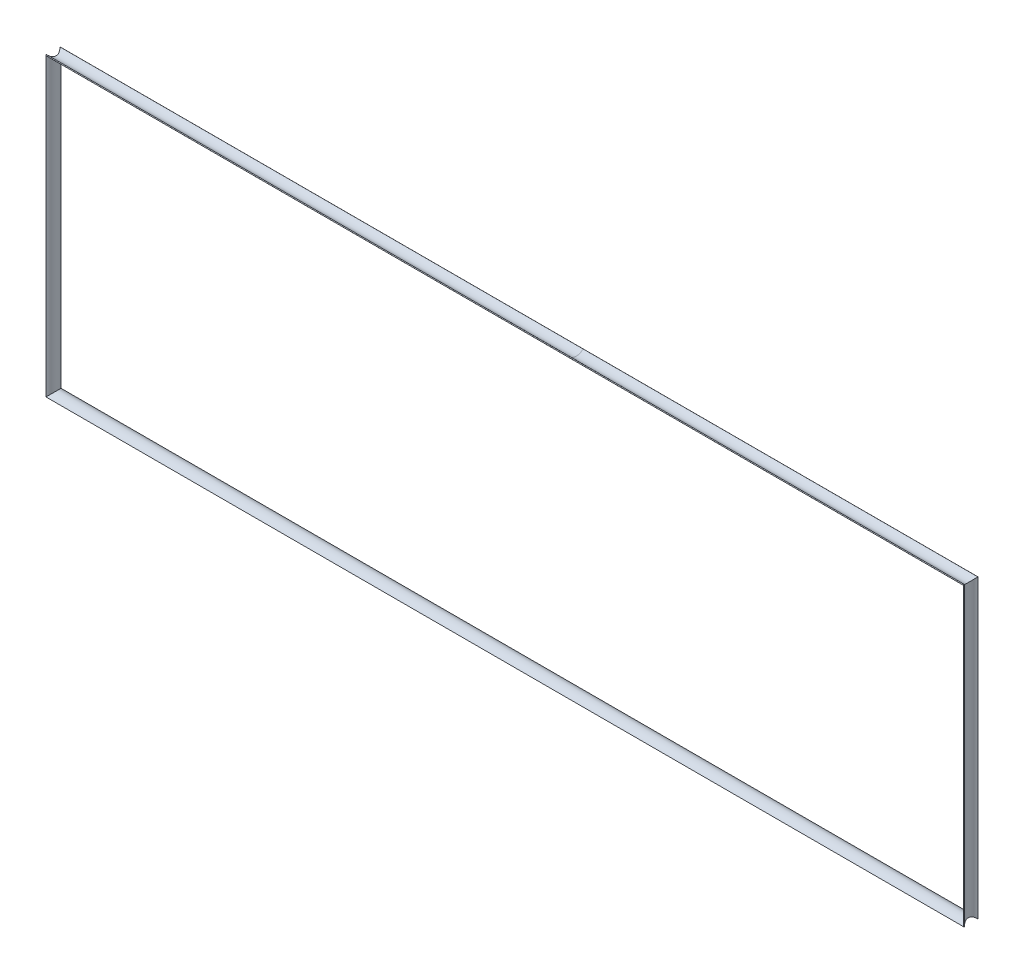
SolidWorks part; units mm, degrees
ref_plane "Front Plane" through (0, 0, 0) normal (0, 0, 1) x (1, 0, 0)
ref_plane "Top Plane" through (0, 0, 0) normal (0, 1, 0) x (1, 0, 0)
ref_plane "Right Plane" through (0, 0, 0) normal (1, 0, 0) x (0, 0, -1)
sketch "Sketch6" plane through (0, 0, 0) normal (0, 0, 1) x (1, 0, 0)
  line L0 (-194.9333, 26.8762) -> (-194.9333, -83.1238)
  line L1 (-194.9333, -83.1238) -> (147.0667, -83.1238)
  line L2 (147.0667, -83.1238) -> (147.0667, 26.8762)
  line L3 (147.0667, 26.8762) -> (-194.9333, 26.8762)
  dimension "D1" = 342
  dimension "D2" = 110
sketch "Sketch7" plane through (0, 0, 0) normal (1, 0, 0) x (0, 0, -1)
  line L0 (2.728, 26.9453) -> (2.4972, 27.1549)
  line L1 (-2.5578, 27.2235) -> (-2.7989, 27.0257)
  arc A1 (-2.7989, 27.0257) -> (2.728, 26.9453) centre (0, 29.4231) ccw
  arc A2 (2.4972, 27.1549) -> (-2.5578, 27.2235) centre (0, 29.4231) cw
sweep "Sweep1" add profiles "Sketch7" path "Sketch6"
